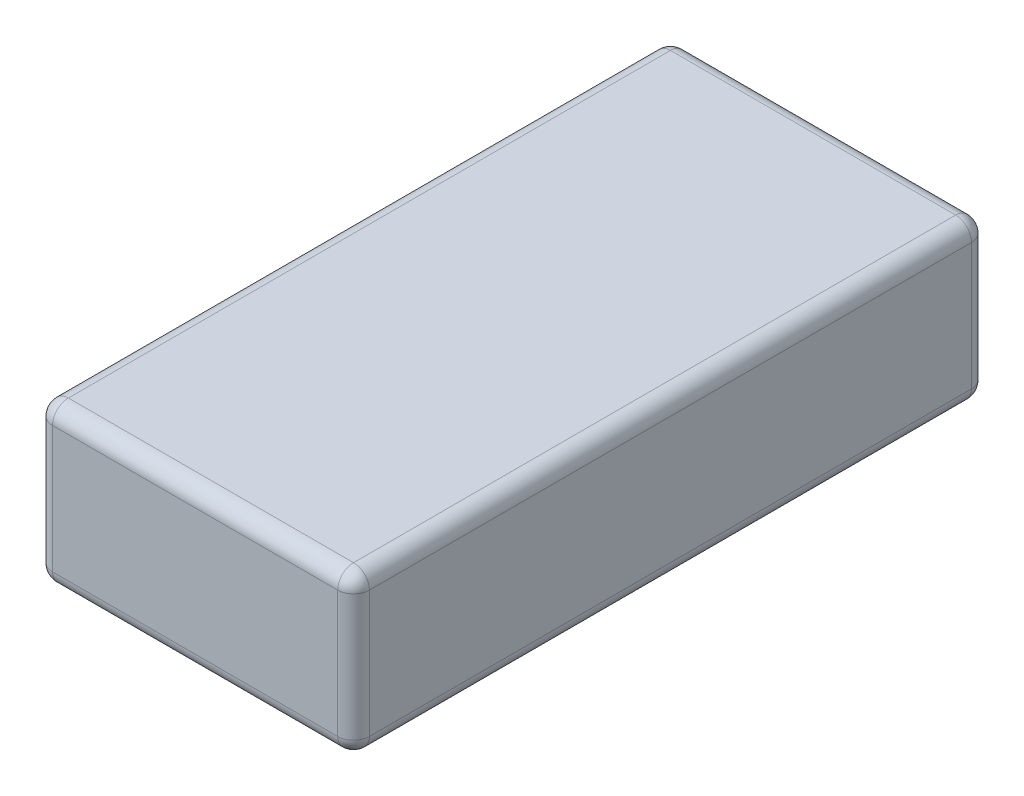
SolidWorks part; units mm, degrees
ref_plane "Front Plane" through (0, 0, 0) normal (0, 0, 1) x (1, 0, 0)
ref_plane "Top Plane" through (0, 0, 0) normal (0, 1, 0) x (1, 0, 0)
ref_plane "Right Plane" through (0, 0, 0) normal (1, 0, 0) x (0, 0, -1)
sketch "Sketch1" plane through (0, 0, 0) normal (0, 1, 0) x (1, 0, 0)
  line L1 (5, -10) -> (-5, -10)
  line L2 (5, -10) -> (5, 10)
  line L3 (5, 10) -> (-5, 10)
  line L4 (-5, -10) -> (-5, 10)
  line L5 (5, -10) -> (-5, 10) construction
  line L6 (5, 10) -> (-5, -10) construction
  point P0 (0, 0)
  dimension "D1" = 10
  dimension "D2" = 20
extrude "Boss-Extrude1" add sketch "Sketch1" along normal blind 5
fillet "Fillet1" radius 0.5 12 edges at (-5, 2.5, -10) (-5, 2.5, 10) (5, 2.5, 10) (5, 2.5, -10) (0, 0, 10) (5, 0, 0) (0, 0, -10) (-5, 0, 0) (0, 5, -10) (5, 5, 0) (0, 5, 10) (-5, 5, 0)
